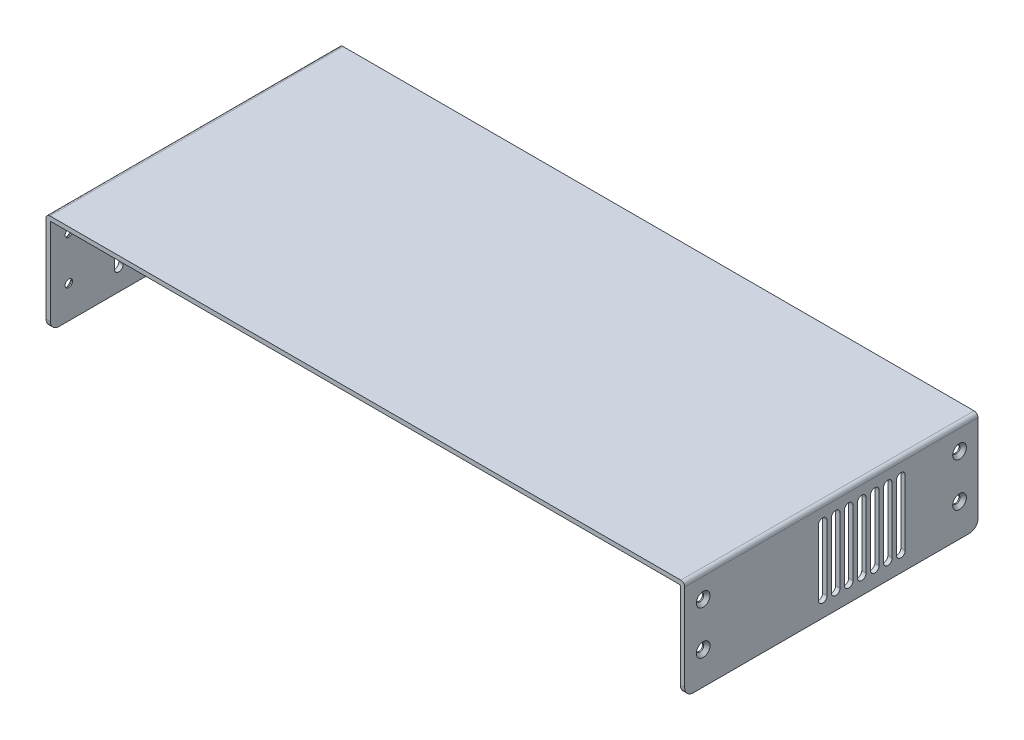
SolidWorks part; units mm, degrees
ref_plane "Front Plane" through (0, 0, 0) normal (0, 0, 1) x (1, 0, 0)
ref_plane "Top Plane" through (0, 0, 0) normal (0, 1, 0) x (1, 0, 0)
ref_plane "Right Plane" through (0, 0, 0) normal (1, 0, 0) x (0, 0, -1)
sketch "Sketch1" plane through (0, 0, 0) normal (0, 0, 1) x (1, 0, 0)
  line L0 (0, 0) -> (-2, 0)
  line L1 (-2, 0) -> (-2, 44.2)
  line L2 (-0.2, 46) -> (290.2, 46)
  line L3 (292, 44.2) -> (292, 0)
  line L4 (292, 0) -> (290, 0)
  line L5 (290, 0) -> (290, 43.5)
  line L6 (289.5, 44) -> (0.5, 44)
  line L7 (0, 43.5) -> (0, 0)
  arc A0 (290, 43.5) -> (289.5, 44) centre (289.5, 43.5) ccw
  arc A1 (0.5, 44) -> (0, 43.5) centre (0.5, 43.5) ccw
  arc A2 (-2, 44.2) -> (-0.2, 46) centre (-0.2, 44.2) cw
  arc A3 (290.2, 46) -> (292, 44.2) centre (290.2, 44.2) cw
  point P13 (0, 44)
  dimension "D5" = 0.5
  dimension "D6" = 1.8
  dimension "D1" = 44
  dimension "D2" = 290
  dimension "D3" = 2
  dimension "D4" = 2
extrude "Boss-Extrude1" add sketch "Sketch1" along normal blind 135
hole_wizard "CSK for M3 Flat Head Machine Screw1" positions "Sketch3" profile "Sketch2" countersink size "M3" standard "Ansi Metric"
sketch "Sketch3" plane through (-2, 0, 0) normal (-1, 0, 0) x (0, 0, 1)
  point P0 (8.5, 35)
  point P1 (8.5, 15)
  point P3 (126.5, 35)
  point P5 (126.5, 15)
sketch "Sketch2" plane through (-2, 35, 8.5) normal (0, 1, 0) x (0, 0, 1)
  line L0 (0, 0) -> (0, 6.0215)
  line L1 (0, 6.0215) -> (1.7, 5)
  line L2 (1.7, 5) -> (1.7, 1.45)
  line L3 (1.7, 1.45) -> (3.15, 0)
  line L5 (3.15, 0) -> (0, 0)
  line L6 (-1.7, 1.45) -> (-3.15, 0) construction
  line L10 (0, 6.0215) -> (-1.7, 5) construction
  line L11 (0, -6.35) -> (0, 107.95) construction
  dimension "Hole Dia." = 3.4
  dimension "Hole Depth" = 5
  dimension "Near C'Sink Dia." = 6.3
  dimension "Near C'Sink Angle" = 90
  dimension "Drill Angle" = 118
hole_wizard "CSK for M3 Flat Head Machine Screw2" positions "Sketch5" profile "Sketch4" countersink size "M3" standard "Ansi Metric"
sketch "Sketch5" plane through (292, 0, 0) normal (1, 0, 0) x (0, 0, -1)
  point P0 (-126.5, 35)
  point P1 (-126.5, 15)
  point P3 (-8.5, 35)
  point P5 (-8.5, 15)
sketch "Sketch4" plane through (292, 35, 126.5) normal (0, 1, 0) x (0, 0, -1)
  line L0 (0, 0) -> (0, 6.0215)
  line L1 (0, 6.0215) -> (1.7, 5)
  line L2 (1.7, 5) -> (1.7, 1.45)
  line L3 (1.7, 1.45) -> (3.15, 0)
  line L5 (3.15, 0) -> (0, 0)
  line L6 (-1.7, 1.45) -> (-3.15, 0) construction
  line L10 (0, 6.0215) -> (-1.7, 5) construction
  line L11 (0, -6.35) -> (0, 107.95) construction
  dimension "Hole Dia." = 3.4
  dimension "Hole Depth" = 5
  dimension "Near C'Sink Dia." = 6.3
  dimension "Near C'Sink Angle" = 90
  dimension "Drill Angle" = 118
fillet "Fillet1" radius 4 4 edges at (291, 0, 135) (291, 0, 0) (-1, 0, 135) (-1, 0, 0)
sketch "Sketch6" plane through (-2, 0, 0) normal (1, 0, 0) x (0, 0, -1)
  line L0 (-103.5, 36) -> (-103.5, 10) construction
  line L1 (-101.5, 36) -> (-101.5, 10)
  line L2 (-105.5, 36) -> (-105.5, 10)
  line L3 (-135, 4) -> (-135, 44.2) construction
  line L4 (-135, 46) -> (0, 46) construction
  line L5 (-131, 0) -> (-4, 0) construction
  arc A0 (-101.5, 36) -> (-105.5, 36) centre (-103.5, 36) ccw
  arc A1 (-105.5, 10) -> (-101.5, 10) centre (-103.5, 10) ccw
  point P2 (-103.5, 23)
  dimension "D1" = 4
  dimension "D2" = 31.5
  dimension "D3" = 10
  dimension "D4" = 10
extrude "Cut-Extrude1" cut sketch "Sketch6" along normal blind 10
pattern_linear "LPattern1" count 13 spacing 6 along (0, 0, -1) of "Cut-Extrude1"
sketch "Sketch7" plane through (292, 0, 0) normal (1, 0, 0) x (0, 0, -1)
  line L0 (-35.5, 38) -> (-35.5, 8) construction
  line L1 (-33.5, 38) -> (-33.5, 8)
  line L2 (-37.5, 38) -> (-37.5, 8)
  line L3 (0, 4) -> (0, 44.2) construction
  line L5 (-131, 0) -> (-4, 0) construction
  line L6 (-135, 46) -> (0, 46) construction
  arc A0 (-33.5, 38) -> (-37.5, 38) centre (-35.5, 38) ccw
  arc A1 (-37.5, 8) -> (-33.5, 8) centre (-35.5, 8) ccw
  point P2 (-35.5, 23)
  point P11 (-66.2773, 44.2)
  dimension "D1" = 35.5
  dimension "D2" = 8
  dimension "D3" = 8
  dimension "D4" = 4
extrude "Cut-Extrude2" cut sketch "Sketch7" against normal blind 10
pattern_linear "LPattern2" count 7 spacing 6 along (0, 0, 1) of "Cut-Extrude2"
